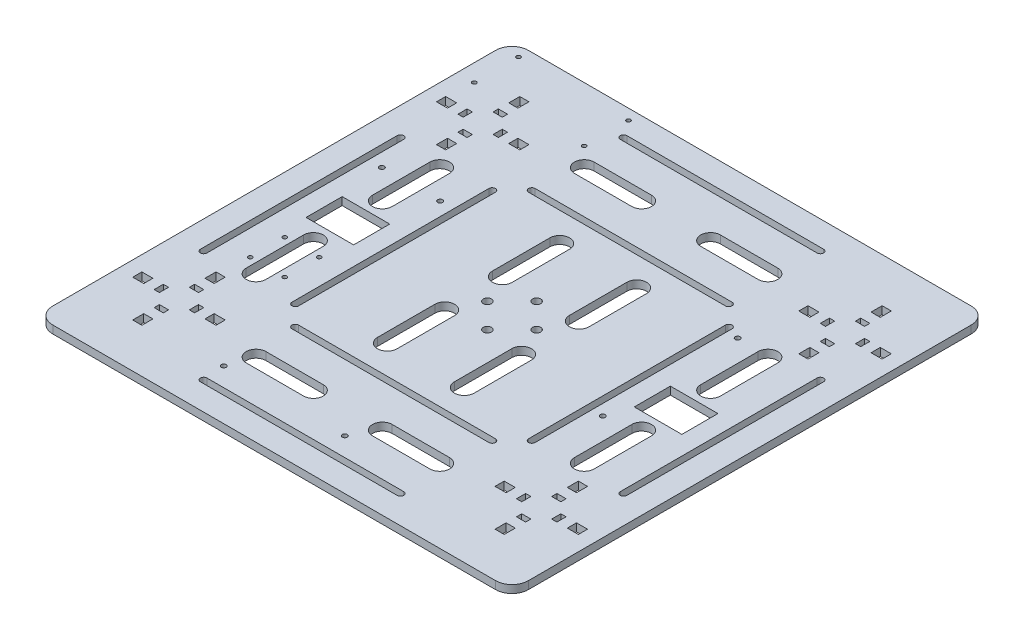
SolidWorks part; units mm, degrees
ref_plane "Front Plane" through (0, 0, 0) normal (0, 0, 1) x (1, 0, 0)
ref_plane "Top Plane" through (0, 0, 0) normal (0, 1, 0) x (1, 0, 0)
ref_plane "Right Plane" through (0, 0, 0) normal (1, 0, 0) x (0, 0, -1)
sketch "Sketch1" plane through (0, 0, 0) normal (0, 1, 0) x (1, 0, 0)
  line L1 (145, -145) -> (-145, -145)
  line L2 (145, -145) -> (145, 145)
  line L3 (145, 145) -> (-145, 145)
  line L4 (-145, -145) -> (-145, 145)
  line L5 (145, -145) -> (-145, 145) construction
  line L6 (145, 145) -> (-145, -145) construction
  point P0 (0, 0)
  dimension "D1" = 290
extrude "Boss-Extrude1" add sketch "Sketch1" along normal blind 4.7625
fillet "Fillet1" radius 10 4 edges at (145, 2.3813, -145) (-145, 2.3813, -145) (-145, 2.3813, 145) (145, 2.3813, 145)
sketch "Sketch3" plane through (0, 4.7625, 0) normal (0, 1, 0) x (1, 0, 0)
  line L0 (-145, 135) -> (-145, -135) construction
  line L1 (-113.25, 118) -> (-107.662, 118)
  line L2 (-113.25, 118) -> (-113.25, 111.269)
  line L3 (-113.25, 111.269) -> (-107.662, 111.269)
  line L4 (-107.662, 118) -> (-107.662, 111.269)
  line L5 (135, 145) -> (-135, 145) construction
  line L6 (-85.056, 95.394) -> (-91.787, 95.394)
  line L7 (-85.056, 95.394) -> (-85.056, 89.806)
  line L8 (-85.056, 89.806) -> (-91.787, 89.806)
  line L9 (-91.787, 95.394) -> (-91.787, 89.806)
  line L10 (-107.662, 67.2) -> (-107.662, 73.931)
  line L11 (-107.662, 67.2) -> (-113.25, 67.2)
  line L12 (-113.25, 67.2) -> (-113.25, 73.931)
  line L13 (-107.662, 73.931) -> (-113.25, 73.931)
  line L14 (-135.856, 89.806) -> (-129.125, 89.806)
  line L15 (-135.856, 89.806) -> (-135.856, 95.394)
  line L16 (-135.856, 95.394) -> (-129.125, 95.394)
  line L17 (-129.125, 89.806) -> (-129.125, 95.394)
  line L18 (-107.662, 104.925) -> (-113.25, 104.925)
  line L19 (-122.781, 95.394) -> (-119.581, 95.394)
  line L20 (-122.781, 95.394) -> (-122.781, 89.806)
  line L21 (-122.781, 89.806) -> (-119.581, 89.806)
  line L22 (-119.581, 95.394) -> (-119.581, 89.806)
  line L23 (-107.662, 104.925) -> (-107.662, 101.725)
  line L24 (-107.662, 101.725) -> (-113.25, 101.725)
  line L25 (-113.25, 104.925) -> (-113.25, 101.725)
  line L26 (-98.131, 89.806) -> (-98.131, 95.394)
  line L27 (-98.131, 89.806) -> (-101.331, 89.806)
  line L28 (-101.331, 89.806) -> (-101.331, 95.394)
  line L29 (-98.131, 95.394) -> (-101.331, 95.394)
  line L30 (-113.25, 80.275) -> (-107.662, 80.275)
  line L31 (-113.25, 80.275) -> (-113.25, 83.475)
  line L32 (-113.25, 83.475) -> (-107.662, 83.475)
  line L33 (-107.662, 80.275) -> (-107.662, 83.475)
  point P8 (-110.456, 92.6)
  point P9 (-110.456, 111.269)
  point P25 (-110.456, 92.6)
  point P42 (-110.456, 92.6)
  dimension "D1" = 5.588
  dimension "D2" = 6.731
  dimension "D3" = 31.75
  dimension "D4" = 27
  dimension "D5" = 25.4
  dimension "D7" = 3.2
  dimension "D8" = 13.075
  dimension "D6" = 4
  dimension "D9" = 4
extrude "Cut-Extrude1" cut sketch "Sketch3" against normal up to surface (4.7625 mm away) up to face at (0, 0, 0)
mirror "Mirror1" about plane through (0, 0, 0) normal (0, 0, 1) of "Cut-Extrude1"
mirror "Mirror2" about plane through (0, 0, 0) normal (1, 0, 0) of "Mirror1", "Cut-Extrude1"
sketch "Sketch4" plane through (0, 4.7625, 0) normal (0, 1, 0) x (1, 0, 0)
  line L0 (-60, 128) -> (60, 128) construction
  line L1 (-60, 130) -> (60, 130)
  line L2 (-60, 126) -> (60, 126)
  line L3 (135, 145) -> (-135, 145) construction
  line L4 (-60, 72.12) -> (60, 72.12) construction
  line L5 (-60, 74.12) -> (60, 74.12)
  line L6 (-60, 70.12) -> (60, 70.12)
  line L7 (128, 60) -> (128, -60) construction
  line L8 (130, 60) -> (130, -60)
  line L9 (126, 60) -> (126, -60)
  line L10 (72.12, 60) -> (72.12, -60) construction
  line L11 (74.12, 60) -> (74.12, -60)
  line L12 (70.12, 60) -> (70.12, -60)
  line L13 (60, -128) -> (-60, -128) construction
  line L14 (60, -130) -> (-60, -130)
  line L15 (60, -126) -> (-60, -126)
  line L16 (60, -72.12) -> (-60, -72.12) construction
  line L17 (60, -74.12) -> (-60, -74.12)
  line L18 (60, -70.12) -> (-60, -70.12)
  line L19 (-128, -60) -> (-128, 60) construction
  line L20 (-130, -60) -> (-130, 60)
  line L21 (-126, -60) -> (-126, 60)
  line L22 (-72.12, -60) -> (-72.12, 60) construction
  line L23 (-74.12, -60) -> (-74.12, 60)
  line L24 (-70.12, -60) -> (-70.12, 60)
  arc A0 (-60, 130) -> (-60, 126) centre (-60, 128) ccw
  arc A1 (60, 126) -> (60, 130) centre (60, 128) ccw
  arc A2 (-60, 74.12) -> (-60, 70.12) centre (-60, 72.12) ccw
  arc A3 (60, 70.12) -> (60, 74.12) centre (60, 72.12) ccw
  arc A4 (130, 60) -> (126, 60) centre (128, 60) ccw
  arc A5 (126, -60) -> (130, -60) centre (128, -60) ccw
  arc A6 (74.12, 60) -> (70.12, 60) centre (72.12, 60) ccw
  arc A7 (70.12, -60) -> (74.12, -60) centre (72.12, -60) ccw
  arc A8 (60, -130) -> (60, -126) centre (60, -128) ccw
  arc A9 (-60, -126) -> (-60, -130) centre (-60, -128) ccw
  arc A10 (60, -74.12) -> (60, -70.12) centre (60, -72.12) ccw
  arc A11 (-60, -70.12) -> (-60, -74.12) centre (-60, -72.12) ccw
  arc A12 (-130, -60) -> (-126, -60) centre (-128, -60) ccw
  arc A13 (-126, 60) -> (-130, 60) centre (-128, 60) ccw
  arc A14 (-74.12, -60) -> (-70.12, -60) centre (-72.12, -60) ccw
  arc A15 (-70.12, 60) -> (-74.12, 60) centre (-72.12, 60) ccw
  point P2 (0, 128)
  point P9 (0, 72.12)
  point P22 (128, 0)
  point P27 (72.12, 0)
  point P36 (0, -128)
  point P41 (0, -72.12)
  point P50 (-128, 0)
  point P55 (-72.12, 0)
  point P62 (0, 0)
  dimension "D1" = 2
  dimension "D2" = 15
  dimension "D3" = 120
  dimension "D4" = 55.88
  dimension "D5" = 4
extrude "Cut-Extrude2" cut sketch "Sketch4" against normal up to surface (4.7625 mm away) up to face at (110.456, 0, -81.875)
sketch "Sketch5" plane through (0, 4.7625, 0) normal (0, 1, 0) x (1, 0, 0)
  line L0 (-126, -60) -> (-126, 60) construction
  line L1 (-114.56, 11) -> (-85.56, 11)
  line L2 (-114.56, 11) -> (-114.56, -11)
  line L3 (-114.56, -11) -> (-85.56, -11)
  line L4 (-85.56, 11) -> (-85.56, -11)
  line L5 (-126, -60) -> (-126, 60) construction
  line L6 (-74.12, 60) -> (-74.12, -60) construction
  line L7 (-74.12, 60) -> (-74.12, -60) construction
  line L8 (-74.12, 0) -> (-126, 0) construction
  line L9 (0, -145) -> (0, 145) construction
  line L10 (135, 145) -> (-135, 145) construction
  line L11 (114.56, -11) -> (85.56, -11)
  line L12 (85.56, 11) -> (85.56, -11)
  line L13 (114.56, 11) -> (85.56, 11)
  line L14 (114.56, 11) -> (114.56, -11)
  point P6 (-114.56, 0)
  point P7 (-126, 0)
  point P12 (-100.06, 0)
  point P13 (-100.06, 11)
  point P20 (0, 0)
  dimension "D1" = 29
  dimension "D2" = 22
extrude "Cut-Extrude3" cut sketch "Sketch5" against normal up to surface (4.7625 mm away) up to face at (0, 0, -128)
sketch "Sketch6" plane through (0, 4.7625, 0) normal (0, 1, 0) x (1, 0, 0)
  line L0 (-56, 100.06) -> (-21, 100.06) construction
  line L1 (-56, 106.06) -> (-21, 106.06)
  line L2 (-56, 94.06) -> (-21, 94.06)
  line L3 (21, 100.06) -> (56, 100.06) construction
  line L4 (21, 106.06) -> (56, 106.06)
  line L5 (21, 94.06) -> (56, 94.06)
  line L6 (-60, 126) -> (60, 126) construction
  line L7 (94.06, 56) -> (94.06, 21)
  line L8 (106.06, 56) -> (106.06, 21)
  line L9 (94.06, -21) -> (94.06, -56)
  line L10 (106.06, -21) -> (106.06, -56)
  line L11 (100.06, 56) -> (100.06, 21) construction
  line L12 (100.06, -21) -> (100.06, -56) construction
  line L13 (56, -94.06) -> (21, -94.06)
  line L14 (56, -106.06) -> (21, -106.06)
  line L15 (-21, -94.06) -> (-56, -94.06)
  line L16 (-21, -106.06) -> (-56, -106.06)
  line L17 (56, -100.06) -> (21, -100.06) construction
  line L18 (-21, -100.06) -> (-56, -100.06) construction
  line L19 (-94.06, -56) -> (-94.06, -21)
  line L20 (-106.06, -56) -> (-106.06, -21)
  line L21 (-94.06, 21) -> (-94.06, 56)
  line L22 (-106.06, 21) -> (-106.06, 56)
  line L23 (-100.06, -56) -> (-100.06, -21) construction
  line L24 (-100.06, 21) -> (-100.06, 56) construction
  line L25 (-60, 70.12) -> (60, 70.12) construction
  line L26 (-70.12, -60) -> (-70.12, 60) construction
  line L27 (-60, 70.12) -> (60, 70.12) construction
  line L28 (-70.12, -60) -> (-70.12, 60) construction
  line L29 (-23.4533, 52.56) -> (-23.4533, 17.56) construction
  line L32 (-17.4533, 52.56) -> (-17.4533, 17.56)
  line L33 (-29.4533, 52.56) -> (-29.4533, 17.56)
  line L34 (0, 70.12) -> (0, 0) construction
  line L35 (0, 0) -> (-70.12, 0) construction
  line L36 (23.4533, 52.56) -> (23.4533, 17.56) construction
  line L37 (17.4533, 52.56) -> (17.4533, 17.56)
  line L38 (29.4533, 52.56) -> (29.4533, 17.56)
  line L39 (-23.4533, -52.56) -> (-23.4533, -17.56) construction
  line L40 (-17.4533, -52.56) -> (-17.4533, -17.56)
  line L41 (-29.4533, -52.56) -> (-29.4533, -17.56)
  line L42 (23.4533, -52.56) -> (23.4533, -17.56) construction
  line L43 (17.4533, -52.56) -> (17.4533, -17.56)
  line L44 (29.4533, -52.56) -> (29.4533, -17.56)
  arc A0 (-56, 106.06) -> (-56, 94.06) centre (-56, 100.06) ccw
  arc A1 (-21, 94.06) -> (-21, 106.06) centre (-21, 100.06) ccw
  arc A2 (21, 106.06) -> (21, 94.06) centre (21, 100.06) ccw
  arc A3 (56, 94.06) -> (56, 106.06) centre (56, 100.06) ccw
  arc A4 (60, 126) -> (60, 130) centre (60, 128) ccw construction
  arc A5 (-60, 130) -> (-60, 126) centre (-60, 128) ccw construction
  arc A6 (106.06, 56) -> (94.06, 56) centre (100.06, 56) ccw
  arc A7 (94.06, 21) -> (106.06, 21) centre (100.06, 21) ccw
  arc A8 (106.06, -21) -> (94.06, -21) centre (100.06, -21) ccw
  arc A9 (94.06, -56) -> (106.06, -56) centre (100.06, -56) ccw
  arc A10 (56, -106.06) -> (56, -94.06) centre (56, -100.06) ccw
  arc A11 (21, -94.06) -> (21, -106.06) centre (21, -100.06) ccw
  arc A12 (-21, -106.06) -> (-21, -94.06) centre (-21, -100.06) ccw
  arc A13 (-56, -94.06) -> (-56, -106.06) centre (-56, -100.06) ccw
  arc A14 (-106.06, -56) -> (-94.06, -56) centre (-100.06, -56) ccw
  arc A15 (-94.06, -21) -> (-106.06, -21) centre (-100.06, -21) ccw
  arc A16 (-106.06, 21) -> (-94.06, 21) centre (-100.06, 21) ccw
  arc A17 (-94.06, 56) -> (-106.06, 56) centre (-100.06, 56) ccw
  arc A20 (-17.4533, 52.56) -> (-29.4533, 52.56) centre (-23.4533, 52.56) ccw
  arc A21 (-29.4533, 17.56) -> (-17.4533, 17.56) centre (-23.4533, 17.56) ccw
  arc A22 (17.4533, 52.56) -> (29.4533, 52.56) centre (23.4533, 52.56) cw
  arc A23 (29.4533, 17.56) -> (17.4533, 17.56) centre (23.4533, 17.56) cw
  arc A24 (-17.4533, -52.56) -> (-29.4533, -52.56) centre (-23.4533, -52.56) cw
  arc A25 (-29.4533, -17.56) -> (-17.4533, -17.56) centre (-23.4533, -17.56) cw
  arc A26 (17.4533, -52.56) -> (29.4533, -52.56) centre (23.4533, -52.56) ccw
  arc A27 (29.4533, -17.56) -> (17.4533, -17.56) centre (23.4533, -17.56) ccw
  point P2 (-38.5, 100.06)
  point P7 (38.5, 100.06)
  point P15 (62, 128)
  point P19 (62, 100.06)
  point P24 (-62, 128)
  point P25 (-62, 100.06)
  point P28 (-23.4533, 35.06)
  point P31 (100.06, 38.5)
  point P36 (100.06, -38.5)
  point P45 (38.5, -100.06)
  point P50 (-38.5, -100.06)
  point P59 (-100.06, -38.5)
  point P64 (-100.06, 38.5)
  point P71 (0, 0)
  point P82 (0, 35.06)
  point P86 (23.4533, 35.06)
  point P94 (-23.4533, -35.06)
  point P101 (23.4533, -35.06)
  dimension "D1" = 6
  dimension "D2" = 35
  dimension "D3" = 25.94
  dimension "D5" = 46.6667
  dimension "D4" = 4
extrude "Cut-Extrude4" cut sketch "Sketch6" against normal up to surface (4.7625 mm away) up to face at (-100.06, 0, 0)
sketch "Sketch7" plane through (0, 4.7625, 0) normal (0, 1, 0) x (1, 0, 0)
  circle A0 centre (0, 15) radius 2.5
  circle A1 centre (15, 0) radius 2.5
  circle A2 centre (0, -15) radius 2.5
  circle A3 centre (-15, 0) radius 2.5
  point P12 (0, 0)
  dimension "D1" = 5
  dimension "D2" = 15
  dimension "D3" = 4
extrude "Cut-Extrude5" cut sketch "Sketch7" against normal up to surface (4.7625 mm away) up to face at (38.5, 0, -100.06)
sketch "Sketch9" plane through (0, 4.7625, 0) normal (0, 1, 0) x (1, 0, 0)
  circle A0 centre (-67.5, 111.5) radius 1.25 construction
  circle A1 centre (-67.5, 111.5) radius 1.25
  circle A2 centre (-134.5, 138.5) radius 1.25 construction
  circle A3 centre (-134.5, 111.5) radius 1.25 construction
  circle A4 centre (-67.5, 138.5) radius 1.25 construction
  circle A5 centre (-134.5, 138.5) radius 1.25
  circle A6 centre (-134.5, 111.5) radius 1.25
  circle A7 centre (-67.5, 138.5) radius 1.25
sketch "Sketch10" plane through (0, 4.7625, 0) normal (0, 1, 0) x (1, 0, 0)
  line L0 (135, 145) -> (-135, 145) construction
  line L1 (-134.5, 138.5) -> (-67.5, 138.5) construction
  line L2 (-134.5, 138.5) -> (-134.5, 111.5) construction
  line L3 (-134.5, 111.5) -> (-67.5, 111.5) construction
  line L4 (-67.5, 138.5) -> (-67.5, 111.5) construction
  line L5 (-145, 135) -> (-145, -135) construction
  circle A0 centre (-134.5, 138.5) radius 1.25
  circle A1 centre (-134.5, 111.5) radius 1.25
  circle A2 centre (-67.5, 111.5) radius 1.25
  circle A3 centre (-67.5, 138.5) radius 1.25
  circle A4 centre (-82.31, 38.5) radius 1.5
  circle A5 centre (-117.81, 38.5) radius 1.5
  circle A6 centre (-110.56, -28) radius 1.25
  circle A7 centre (-110.56, -49) radius 1.25
  circle A8 centre (-89.56, -28) radius 1.25
  circle A9 centre (-89.56, -49) radius 1.25
  circle A10 centre (-61.25, -114.5) radius 1.5
  circle A11 centre (12.55, -114.5) radius 1.5
  circle A12 centre (80.756, 56.8322) radius 1.5
  circle A13 centre (80.756, -25.4149) radius 1.5
  dimension "D1" = 2.5
  dimension "D6" = 3
  dimension "D7" = 2.5
  dimension "D8" = 3
  dimension "D9" = 3
  dimension "D2" = 67
  dimension "D3" = 27
  dimension "D4" = 6.5
  dimension "D5" = 10.5
extrude "Cut-Extrude6" cut sketch "Sketch10" against normal up to surface (4.7625 mm away) up to face at (0, 0, -12.5)
